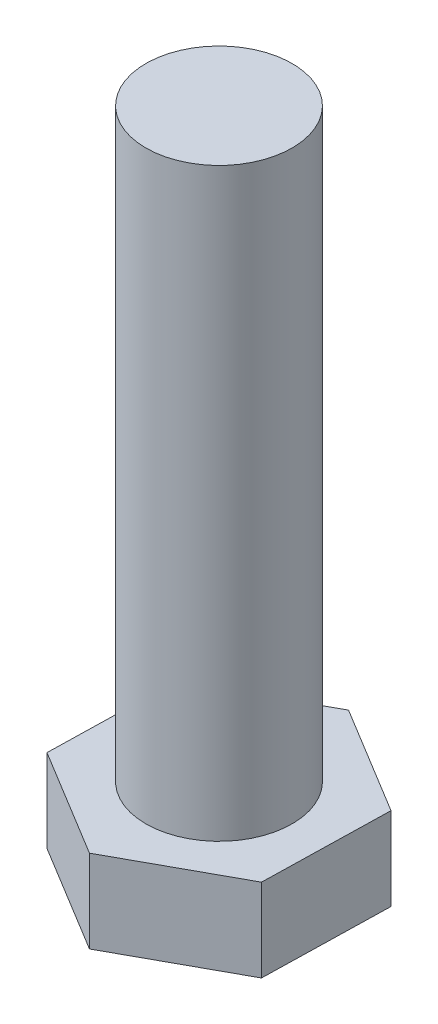
SolidWorks part; units mm, degrees
ref_plane "Спереди" through (0, 0, 0) normal (0, 0, 1) x (1, 0, 0)
ref_plane "Сверху" through (0, 0, 0) normal (0, 1, 0) x (1, 0, 0)
ref_plane "Справа" through (0, 0, 0) normal (1, 0, 0) x (0, 0, -1)
sketch "Эскиз1" plane through (0, 0, 0) normal (0, 1, 0) x (1, 0, 0)
  line L1 (14.8016, -8.9952) -> (15.1908, 8.321)
  line L2 (15.1908, 8.321) -> (0.3893, 17.3161)
  line L3 (0.3893, 17.3161) -> (-14.8016, 8.9952)
  line L4 (-14.8016, 8.9952) -> (-15.1908, -8.321)
  line L5 (-15.1908, -8.321) -> (-0.3893, -17.3161)
  line L6 (-0.3893, -17.3161) -> (14.8016, -8.9952)
  circle A0 centre (0, 0) radius 15 construction
extrude "Бобышка-Вытянуть1" add sketch "Эскиз1" along normal blind 12.5
sketch "Эскиз2" plane through (0, 12.5, 0) normal (0, 1, 0) x (1, 0, 0)
  circle A0 centre (0, 0) radius 10
extrude "Бобышка-Вытянуть2" add sketch "Эскиз2" along normal blind 80
chamfer "Фаска1" distance 2 angle 30 6 edges at (7.79, 0, -12.8185) (14.9962, 0, 0.3371) (7.2062, 0, 13.1557) (-7.79, 0, 12.8185) (-14.9962, 0, -0.3371) (-7.2062, 0, -13.1557)
